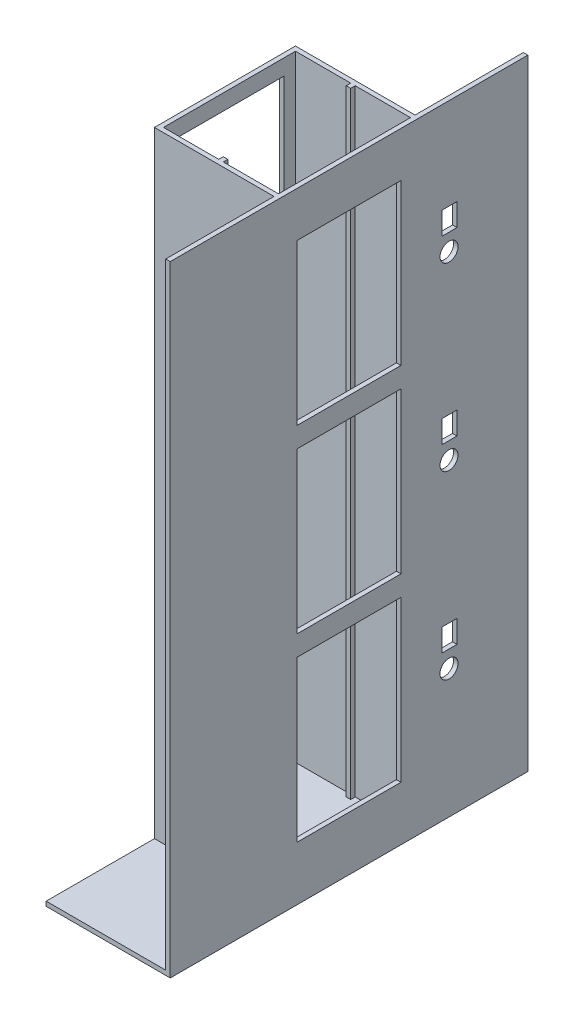
SolidWorks part; units mm, degrees
ref_plane "Plan de face" through (0, 0, 0) normal (0, 0, 1) x (1, 0, 0)
ref_plane "Plan de dessus" through (0, 0, 0) normal (0, 1, 0) x (1, 0, 0)
ref_plane "Plan de droite" through (0, 0, 0) normal (1, 0, 0) x (0, 0, -1)
sketch "Esquisse1" plane through (0, 0, 0) normal (0, 0, 1) x (1, 0, 0)
  line L1 (0, 0) -> (102, 0)
  line L2 (0, 0) -> (0, 546)
  line L3 (0, 546) -> (102, 546)
  line L4 (102, 0) -> (102, 546)
  dimension "D1" = 102
  dimension "D2" = 546
extrude "Boss.-Extru.1" add sketch "Esquisse1" along normal blind 125
sketch "Esquisse2" plane through (102, 0, 0) normal (1, 0, 0) x (0, 0, -1)
  line L0 (-125, 0) -> (0, 0) construction
  line L1 (-121, 0) -> (-4, 0)
  line L2 (-121, 0) -> (-121, 546)
  line L3 (-121, 546) -> (-4, 546)
  line L4 (-4, 0) -> (-4, 546)
  line L5 (-125, 546) -> (0, 546) construction
  line L6 (-125, 0) -> (-125, 546) construction
  dimension "D1" = 117
  dimension "D2" = 4
extrude "Enlèv. mat.-Extru.1" cut sketch "Esquisse2" against normal through all
sketch "Esquisse3" plane through (0, 0, 121) normal (0, 0, -1) x (-1, 0, 0)
  line L0 (0, 0) -> (-102, 0) construction
  line L1 (-53, 0) -> (-49, 0)
  line L2 (-53, 0) -> (-53, 546)
  line L3 (-53, 546) -> (-49, 546)
  line L4 (-49, 0) -> (-49, 546)
  line L5 (-102, 546) -> (0, 546) construction
  line L6 (-102, 0) -> (-102, 546) construction
  dimension "D1" = 49
  dimension "D2" = 4
extrude "Boss.-Extru.2" add sketch "Esquisse3" along normal blind 4
sketch "Esquisse4" plane through (0, 0, 4) normal (0, 0, 1) x (1, 0, 0)
  line L0 (0, 0) -> (102, 0) construction
  line L1 (49, 0) -> (53, 0)
  line L2 (49, 0) -> (49, 546)
  line L3 (49, 546) -> (53, 546)
  line L4 (53, 0) -> (53, 546)
  line L5 (102, 546) -> (0, 546) construction
  line L6 (0, 546) -> (0, 0) construction
  dimension "D1" = 49
  dimension "D2" = 4
extrude "Boss.-Extru.3" add sketch "Esquisse4" along normal blind 4
sketch "Esquisse5" plane through (0, 0, 0) normal (-1, 0, 0) x (0, 0, 1)
  line L0 (0, 546) -> (0, 0) construction
  line L1 (0, 0) -> (125, 0)
  line L2 (0, 0) -> (0, 546)
  line L3 (0, 546) -> (125, 546)
  line L4 (125, 0) -> (125, 546)
  dimension "D1" = 0
extrude "Boss.-Extru.4" add sketch "Esquisse5" along normal blind 4
sketch "Esquisse6" plane through (-4, 0, 0) normal (-1, 0, 0) x (0, 0, 1)
  line L0 (0, 546) -> (0, 0) construction
  line L1 (14, 14) -> (111, 14)
  line L2 (14, 14) -> (14, 532)
  line L3 (14, 532) -> (111, 532)
  line L4 (111, 14) -> (111, 532)
  line L5 (125, 0) -> (125, 546) construction
  line L6 (0, 0) -> (125, 0) construction
  line L7 (125, 546) -> (0, 546) construction
  dimension "D1" = 14
  dimension "D2" = 14
  dimension "D3" = 14
  dimension "D4" = 14
extrude "Enlèv. mat.-Extru.2" cut sketch "Esquisse6" against normal through all
sketch "Esquisse7" plane through (102, 0, 0) normal (1, 0, 0) x (0, 0, -1)
  line L1 (96, 0) -> (-221, 0)
  line L2 (96, 0) -> (96, 546)
  line L3 (96, 546) -> (-221, 546)
  line L4 (-221, 0) -> (-221, 546)
  line L7 (-125, 0) -> (-125, 546) construction
  point P4 (-62.5, 0)
  dimension "D1" = 546
  dimension "D2" = 317
  dimension "D3" = 62.5
  dimension "D4" = 96
extrude "Boss.-Extru.5" add sketch "Esquisse7" along normal blind 4
sketch "Esquisse8" plane through (106, 0, 0) normal (1, 0, 0) x (0, 0, -1)
  line L0 (-221, 0) -> (96, 0) construction
  line L1 (-108.5, 44) -> (-16.5, 44)
  line L2 (-108.5, 44) -> (-108.5, 186)
  line L3 (-108.5, 186) -> (-16.5, 186)
  line L4 (-16.5, 44) -> (-16.5, 186)
  line L5 (-108.5, 204) -> (-16.5, 204)
  line L6 (-108.5, 204) -> (-108.5, 346)
  line L7 (-108.5, 346) -> (-16.5, 346)
  line L8 (-16.5, 204) -> (-16.5, 346)
  line L9 (-108.5, 364) -> (-16.5, 364)
  line L10 (-108.5, 364) -> (-108.5, 506)
  line L11 (-108.5, 506) -> (-16.5, 506)
  line L12 (-16.5, 364) -> (-16.5, 506)
  line L13 (-221, 546) -> (-221, 0) construction
  dimension "D1" = 142
  dimension "D2" = 92
  dimension "D3" = 44
  dimension "D4" = 112.5
  dimension "D5" = 142
  dimension "D6" = 92
  dimension "D7" = 112.5
  dimension "D8" = 18
  dimension "D9" = 142
  dimension "D10" = 92
  dimension "D11" = 112.5
  dimension "D12" = 18
extrude "Enlèv. mat.-Extru.3" cut sketch "Esquisse8" against normal through all
sketch "Esquisse10" plane through (106, 0, 0) normal (1, 0, 0) x (0, 0, -1)
  line L0 (-16.5, 44) -> (-16.5, 186) construction
  line L1 (20, 145) -> (33.2, 145)
  line L2 (20, 145) -> (20, 125)
  line L3 (20, 125) -> (33.2, 125)
  line L4 (33.2, 145) -> (33.2, 125)
  line L5 (20, 285) -> (33.2, 285)
  line L6 (20, 285) -> (20, 305)
  line L7 (20, 305) -> (33.2, 305)
  line L8 (33.2, 285) -> (33.2, 305)
  line L9 (20, 445) -> (33.2, 445)
  line L10 (20, 445) -> (20, 465)
  line L11 (20, 465) -> (33.2, 465)
  line L12 (33.2, 445) -> (33.2, 465)
  line L13 (-16.5, 204) -> (-16.5, 346) construction
  line L14 (-16.5, 364) -> (-16.5, 506) construction
  line L15 (-108.5, 44) -> (-16.5, 44) construction
  line L16 (-108.5, 204) -> (-16.5, 204) construction
  line L17 (-108.5, 364) -> (-16.5, 364) construction
  point P18 (26.6, 125)
  dimension "D1" = 20
  dimension "D2" = 13.2
  dimension "D3" = 20
  dimension "D4" = 13.2
  dimension "D5" = 20
  dimension "D6" = 13.2
  dimension "D7" = 36.5
  dimension "D8" = 36.5
  dimension "D9" = 36.5
  dimension "D10" = 81
  dimension "D11" = 81
  dimension "D12" = 81
extrude "Enlèv. mat.-Extru.4" cut sketch "Esquisse10" against normal through all
sketch "Esquisse12" plane through (106, 0, 0) normal (1, 0, 0) x (0, 0, -1)
  line L0 (20, 145) -> (20, 125) construction
  line L1 (-108.5, 44) -> (-16.5, 44) construction
  line L2 (-108.5, 204) -> (-16.5, 204) construction
  line L3 (-108.5, 364) -> (-16.5, 364) construction
  line L4 (20, 305) -> (20, 285) construction
  line L6 (20, 465) -> (20, 445) construction
  circle A0 centre (26.125, 110) radius 8
  circle A1 centre (26.125, 270) radius 8
  circle A2 centre (26.125, 430) radius 8
  dimension "D1" = 16
  dimension "D5" = 16
  dimension "D7" = 16
  dimension "D2" = 66
  dimension "D3" = 6.125
  dimension "D4" = 66
  dimension "D6" = 66
  dimension "D8" = 6.125
  dimension "D9" = 6.125
extrude "Enlèv. mat.-Extru.5" cut sketch "Esquisse12" against normal through all
sketch "Esquisse13" plane through (0, 0, 0) normal (0, -1, 0) x (1, 0, 0)
  line L6 (106, 221) -> (-4, 221)
  line L7 (106, 221) -> (106, -96)
  line L8 (106, -96) -> (-4, -96)
  line L9 (-4, 221) -> (-4, -96)
  dimension "D1" = 110
extrude "Boss.-Extru.6" add sketch "Esquisse13" along normal blind 4
